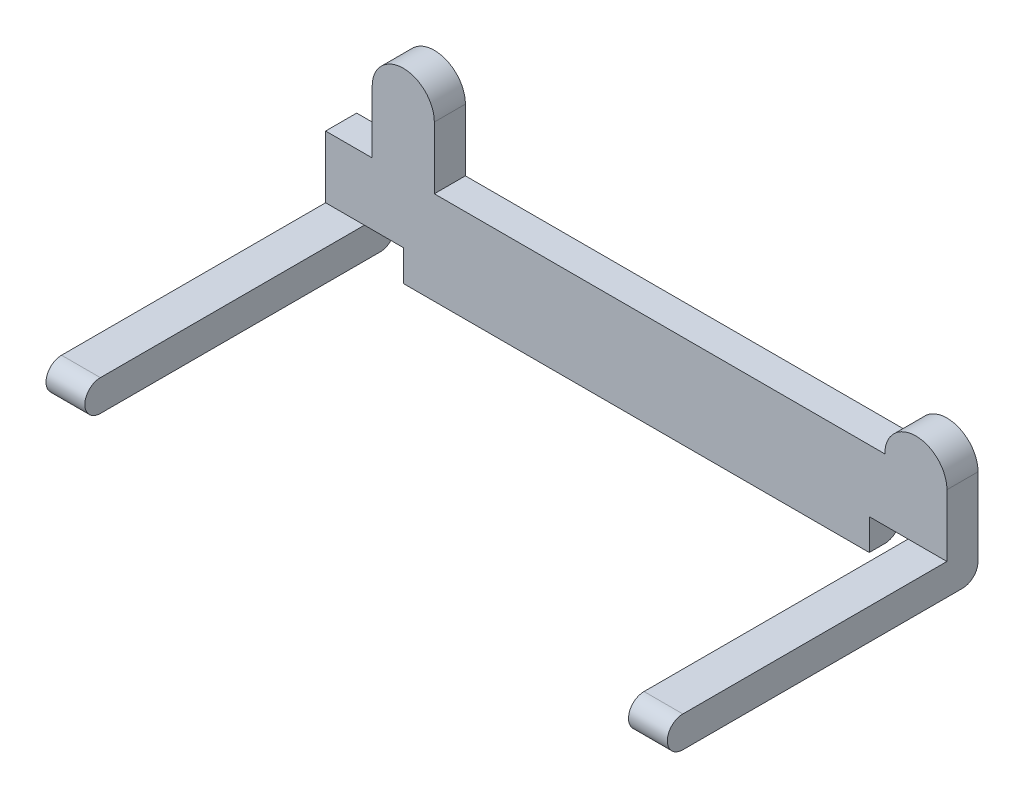
SolidWorks part; units mm, degrees
ref_plane "Front" through (0, 0, 0) normal (0, 0, 1) x (1, 0, 0)
ref_plane "Top" through (0, 0, 0) normal (0, 1, 0) x (1, 0, 0)
ref_plane "Right" through (0, 0, 0) normal (1, 0, 0) x (0, 0, -1)
sketch "草图1" plane through (0, 0, 0) normal (1, 0, 0) x (0, 0, -1)
  line L0 (-18, 0) -> (18, 0) construction
  line L3 (-18, 2) -> (18, 2)
  line L4 (-18, -2) -> (18, -2)
  line L6 (18, 2) -> (20, 2)
  line L7 (20, 2) -> (20, 0)
  arc A6 (-18, 2) -> (-18, -2) centre (-18, 0) ccw
  arc A7 (18, -2) -> (20, 0) centre (18, 0) ccw
  point P2 (0, 0)
  point P4 (0, 0)
extrude "凸台-拉伸1" add sketch "草图1" along normal blind 80
sketch "草图10" plane through (80, 0, 0) normal (1, 0, 0) x (0, 0, -1)
  line L1 (20, 2) -> (16, 2)
  line L2 (20, 2) -> (20, 10)
  line L3 (20, 10) -> (16, 10)
  line L4 (16, 2) -> (16, 10)
  dimension "D1" = 8
  dimension "D2" = 4
extrude "凸台-拉伸8" add sketch "草图10" against normal blind 80
sketch "草图11" plane through (0, 0, -20) normal (0, 0, -1) x (-1, 0, 0)
  line L0 (-40, 10) -> (-40, -15.3556) construction
  line L1 (0, 10) -> (-80, 10) construction
  line L2 (-6, 22.9481) -> (-6, 22) construction
  line L3 (-74, 20.1772) -> (-74, 18) construction
  line L4 (-6, 18) -> (-6, -28.3136) construction
  line L5 (-6, 10) -> (-14, 10)
  line L6 (-6, 10) -> (-6, 18)
  line L8 (-14, 10) -> (-14, 18)
  line L13 (-74, 10) -> (-74, -25.3797) construction
  line L14 (-80, 0) -> (-80, 10) construction
  line L19 (-72, 6) -> (-80, 6)
  line L20 (-72, 6) -> (-72, 10)
  line L22 (-80, 10) -> (-80, 6)
  arc A0 (-6, 18) -> (-14, 18) centre (-10, 18) ccw
  arc A5 (-72, 10) -> (-80, 10) centre (-76, 10) ccw
  dimension "D6" = 8
  dimension "D1" = 34
  dimension "D2" = 34
  dimension "D4" = 12
extrude "凸台-拉伸9" add sketch "草图11" against normal blind 4
sketch "草图12" plane through (0, 2, 0) normal (0, 1, 0) x (1, 0, 0)
  line L0 (0, 16) -> (80, 16) construction
  line L1 (5, 16) -> (75, 16)
  line L2 (5, 16) -> (5, -24.8159)
  line L3 (5, -24.8159) -> (75, -24.8159)
  line L4 (75, 16) -> (75, -24.8159)
  line L5 (40, -20) -> (40, 24.2454) construction
  line L6 (0, -20) -> (80, -20) construction
  dimension "D1" = 70
  dimension "D2" = 35
extrude "切除-拉伸1" cut sketch "草图12" against normal blind 10
sketch "草图13" plane through (0, 0, -16) normal (0, 0, 1) x (1, 0, 0)
  line L0 (75, -2) -> (5, -2) construction
  line L1 (5, 2) -> (10, 2)
  line L2 (5, 2) -> (5, -2)
  line L3 (5, -2) -> (10, -2)
  line L4 (10, 2) -> (10, -2)
  line L6 (75, 2) -> (70, 2)
  line L7 (75, 2) -> (75, -2)
  line L8 (75, -2) -> (70, -2)
  line L9 (70, 2) -> (70, -2)
  dimension "D1" = 5
  dimension "D2" = 5
extrude "切除-拉伸2" cut sketch "草图13" against normal blind 10
